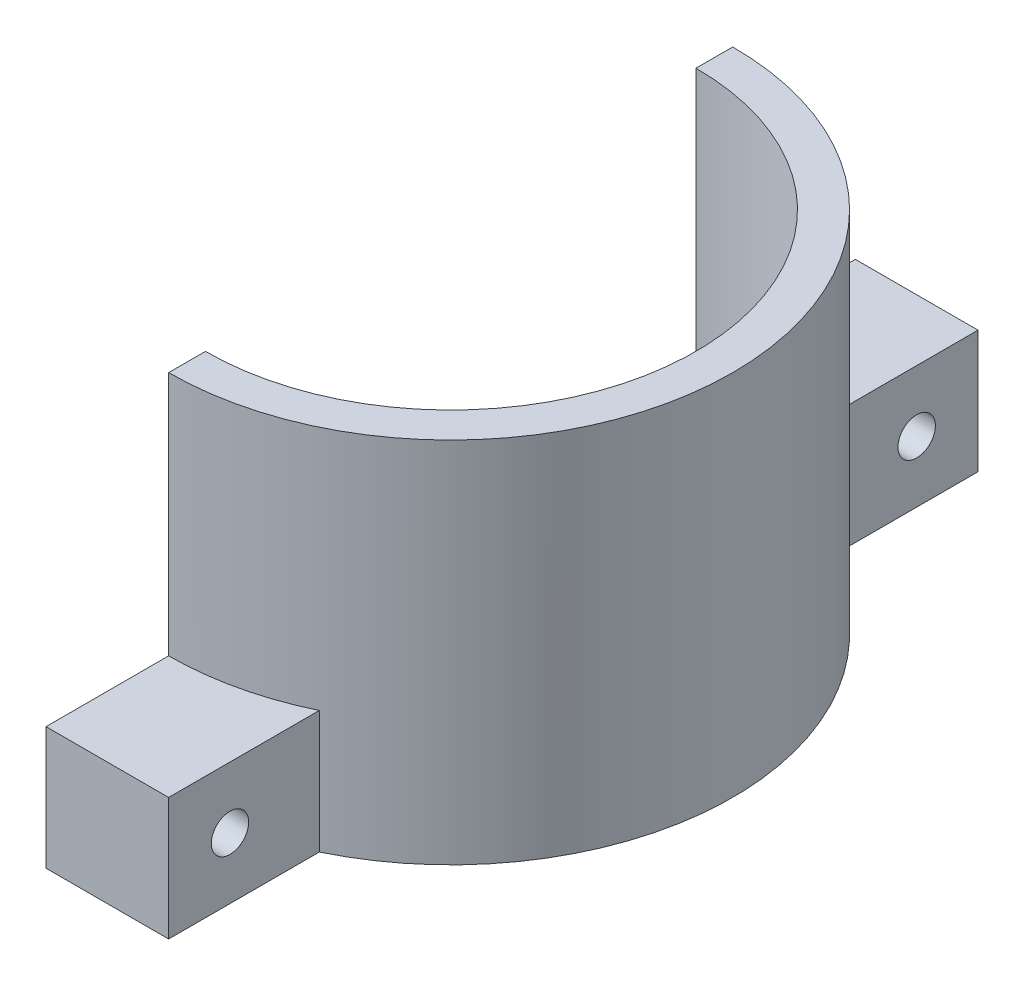
SolidWorks part; units mm, degrees
ref_plane "Front Plane" through (0, 0, 0) normal (0, 0, 1) x (1, 0, 0)
ref_plane "Top Plane" through (0, 0, 0) normal (0, 1, 0) x (1, 0, 0)
ref_plane "Right Plane" through (0, 0, 0) normal (1, 0, 0) x (0, 0, -1)
sketch "Sketch1" plane through (0, 0, 0) normal (0, 1, 0) x (1, 0, 0)
  line L0 (0, 23) -> (0, 20)
  line L1 (0, -20) -> (0, -23)
  arc A0 (0, 20) -> (0, -20) centre (0, 0) cw
  arc A1 (0, 23) -> (0, -23) centre (0, 0) cw
  dimension "D3" = 20
  dimension "D1" = 3
  dimension "D2" = 3
extrude "Tube" add sketch "Sketch1" along normal blind 30
sketch "Sketch2" plane through (0, 0, 0) normal (0, -1, 0) x (-1, 0, 0)
  line L2 (0, -23) -> (0, -33)
  line L3 (0, -33) -> (-10, -33)
  line L4 (-10, -20.7123) -> (-10, -33)
  line L6 (0, 23) -> (0, 33)
  line L7 (0, 33) -> (-10, 33)
  line L8 (-10, 20.7123) -> (-10, 33)
  arc A0 (0, -23) -> (-10, -20.7123) centre (0, 0) cw
  arc A1 (0, 23) -> (-10, 20.7123) centre (0, 0) ccw
  dimension "D1" = 10
  dimension "D2" = 10
  dimension "D3" = 10
  dimension "D4" = 10
extrude "Terminals" add sketch "Sketch2" against normal blind 10
sketch "Sketch3" plane through (0, 0, 0) normal (-1, 0, 0) x (0, 0, 1)
  line L0 (-33, 10) -> (-33, 0) construction
  line L1 (-23, 10) -> (-33, 10) construction
  line L2 (33, 10) -> (33, 0) construction
  line L3 (33, 10) -> (23, 10) construction
  circle A0 centre (-28, 5) radius 1.524
  circle A1 centre (28, 5) radius 1.524
  dimension "D3" = 3.048
  dimension "D6" = 3.048
  dimension "D1" = 5
  dimension "D2" = 5
  dimension "D4" = 5
  dimension "D5" = 5
extrude "Cut-Extrude1" cut sketch "Sketch3" against normal up to next
